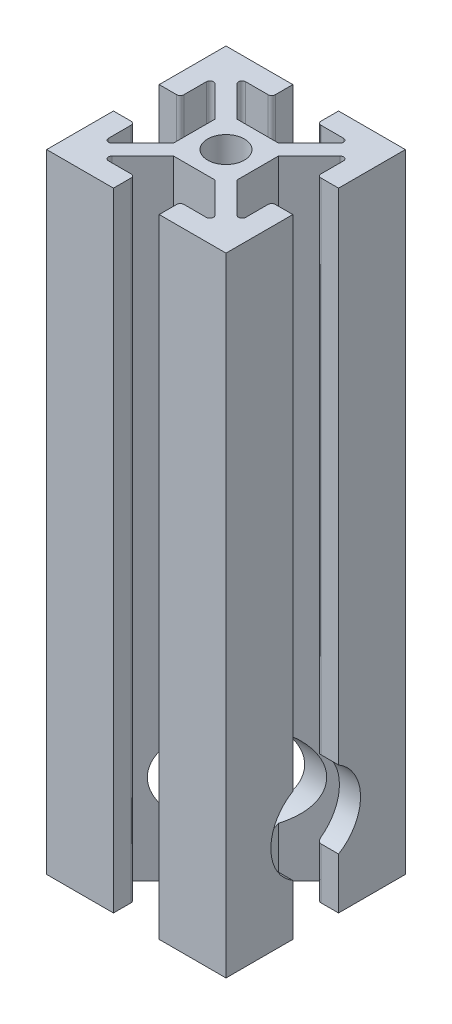
SolidWorks part; units mm, degrees
ref_plane "Front Plane" through (0, 0, 0) normal (0, 0, 1) x (1, 0, 0)
ref_plane "Top Plane" through (0, 0, 0) normal (0, 1, 0) x (1, 0, 0)
ref_plane "Right Plane" through (0, 0, 0) normal (1, 0, 0) x (0, 0, -1)
sketch "Sketch1" plane through (0, 0, 0) normal (0, 1, 0) x (1, 0, 0)
  line L1 (-12.7, 12.7) -> (12.7, 12.7)
  line L2 (-12.7, 12.7) -> (-12.7, -12.7)
  line L3 (-12.7, -12.7) -> (12.7, -12.7)
  line L4 (12.7, 12.7) -> (12.7, -12.7)
  line L5 (-12.7, 12.7) -> (12.7, -12.7) construction
  line L6 (-12.7, -12.7) -> (12.7, 12.7) construction
  point P0 (0, 0)
  dimension "D1" = 25.4
  dimension "D2" = 25.4
extrude "Boss-Extrude1" add sketch "Sketch1" along normal blind 88.9
sketch "Sketch2" plane through (12.7, 0, 0) normal (1, 0, 0) x (0, 0, -1)
  line L0 (-12.7, 0) -> (12.7, 0) construction
  circle A0 centre (0, 12.7) radius 6.35
  point P4 (0, 0)
  dimension "D1" = 12.7
  dimension "D2" = 12.7
extrude "Cut-Extrude1" cut sketch "Sketch2" against normal through all
sketch "Sketch4" plane through (0, 0, 0) normal (0, -1, 0) x (1, 0, 0)
  line L0 (-3.2385, 12.7) -> (3.2385, 12.7)
  line L1 (-12.7, 12.7) -> (12.7, 12.7) construction
  line L2 (3.2385, 12.7) -> (3.2385, 10.2185)
  line L3 (3.7465, 9.7105) -> (6.9215, 9.7105)
  line L4 (7.2807, 8.8433) -> (2.9459, 4.5085)
  line L5 (2.9459, 4.5085) -> (-2.9459, 4.5085)
  line L6 (0, -1000) -> (0, 49000) construction
  line L7 (-7.2807, 8.8433) -> (-2.9459, 4.5085)
  line L8 (-3.7465, 9.7105) -> (-6.9215, 9.7105)
  line L9 (-3.2385, 12.7) -> (-3.2385, 10.2185)
  line L10 (12.7, 3.2385) -> (12.7, -3.2385)
  line L11 (12.7, -3.2385) -> (10.2185, -3.2385)
  line L12 (9.7105, -3.7465) -> (9.7105, -6.9215)
  line L13 (8.8433, -7.2807) -> (4.5085, -2.9459)
  line L14 (4.5085, -2.9459) -> (4.5085, 2.9459)
  line L15 (8.8433, 7.2807) -> (4.5085, 2.9459)
  line L16 (9.7105, 3.7465) -> (9.7105, 6.9215)
  line L17 (12.7, 3.2385) -> (10.2185, 3.2385)
  line L18 (3.2385, -12.7) -> (-3.2385, -12.7)
  line L19 (-3.2385, -12.7) -> (-3.2385, -10.2185)
  line L20 (-3.7465, -9.7105) -> (-6.9215, -9.7105)
  line L21 (-7.2807, -8.8433) -> (-2.9459, -4.5085)
  line L22 (-2.9459, -4.5085) -> (2.9459, -4.5085)
  line L23 (7.2807, -8.8433) -> (2.9459, -4.5085)
  line L24 (3.7465, -9.7105) -> (6.9215, -9.7105)
  line L25 (3.2385, -12.7) -> (3.2385, -10.2185)
  line L26 (-12.7, -3.2385) -> (-12.7, 3.2385)
  line L27 (-12.7, 3.2385) -> (-10.2185, 3.2385)
  line L28 (-9.7105, 3.7465) -> (-9.7105, 6.9215)
  line L29 (-8.8433, 7.2807) -> (-4.5085, 2.9459)
  line L30 (-4.5085, 2.9459) -> (-4.5085, -2.9459)
  line L31 (-8.8433, -7.2807) -> (-4.5085, -2.9459)
  line L32 (-9.7105, -3.7465) -> (-9.7105, -6.9215)
  line L33 (-12.7, -3.2385) -> (-10.2185, -3.2385)
  line L34 (12.7, -12.7) -> (-12.7, -12.7) construction
  line L35 (-12.7, -12.7) -> (-12.7, 12.7) construction
  circle A0 centre (0, 0) radius 2.6035
  arc A1 (6.9215, 9.7105) -> (7.2807, 8.8433) centre (6.9215, 9.2025) cw
  arc A2 (3.2385, 10.2185) -> (3.7465, 9.7105) centre (3.7465, 10.2185) ccw
  arc A3 (-3.2385, 10.2185) -> (-3.7465, 9.7105) centre (-3.7465, 10.2185) cw
  arc A4 (-6.9215, 9.7105) -> (-7.2807, 8.8433) centre (-6.9215, 9.2025) ccw
  arc A5 (9.7105, -6.9215) -> (8.8433, -7.2807) centre (9.2025, -6.9215) cw
  arc A6 (10.2185, -3.2385) -> (9.7105, -3.7465) centre (10.2185, -3.7465) ccw
  arc A7 (10.2185, 3.2385) -> (9.7105, 3.7465) centre (10.2185, 3.7465) cw
  arc A8 (9.7105, 6.9215) -> (8.8433, 7.2807) centre (9.2025, 6.9215) ccw
  arc A9 (-6.9215, -9.7105) -> (-7.2807, -8.8433) centre (-6.9215, -9.2025) cw
  arc A10 (-3.2385, -10.2185) -> (-3.7465, -9.7105) centre (-3.7465, -10.2185) ccw
  arc A11 (3.2385, -10.2185) -> (3.7465, -9.7105) centre (3.7465, -10.2185) cw
  arc A12 (6.9215, -9.7105) -> (7.2807, -8.8433) centre (6.9215, -9.2025) ccw
  arc A13 (-9.7105, 6.9215) -> (-8.8433, 7.2807) centre (-9.2025, 6.9215) cw
  arc A14 (-10.2185, 3.2385) -> (-9.7105, 3.7465) centre (-10.2185, 3.7465) ccw
  arc A15 (-10.2185, -3.2385) -> (-9.7105, -3.7465) centre (-10.2185, -3.7465) cw
  arc A16 (-9.7105, -6.9215) -> (-8.8433, -7.2807) centre (-9.2025, -6.9215) ccw
  point P24 (0, 4.5085)
  point P25 (0, 12.7)
  point P44 (4.5085, 0)
  point P45 (12.7, 0)
  point P62 (0, -4.5085)
  point P63 (0, -12.7)
  point P80 (-4.5085, 0)
  point P81 (-12.7, 0)
  dimension "D1" = 5.207
  dimension "D2" = 0.508
  dimension "D3" = 6.477
  dimension "D4" = 13.843
  dimension "D6" = 2.2098
  dimension "D7" = 9.017
  dimension "D5" = 4
extrude "Cut-Extrude2" cut sketch "Sketch4" against normal through all
